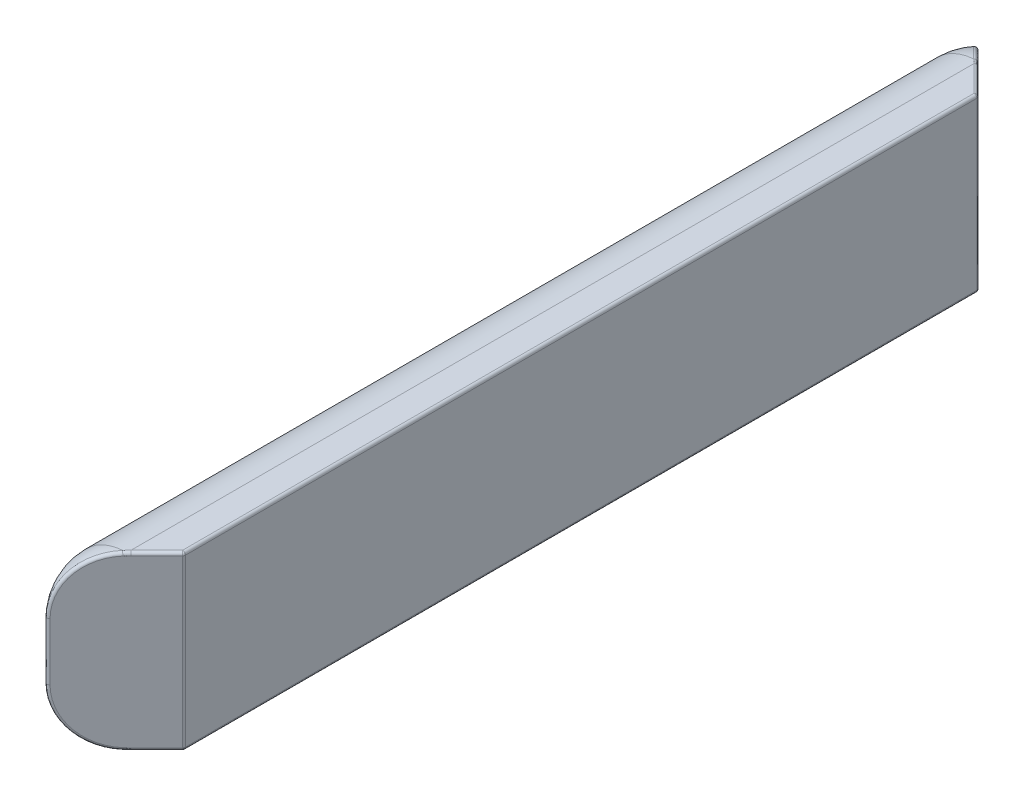
SolidWorks part; units mm, degrees
ref_plane "Front Plane" through (0, 0, 0) normal (0, 0, 1) x (1, 0, 0)
ref_plane "Top Plane" through (0, 0, 0) normal (0, 1, 0) x (1, 0, 0)
ref_plane "Right Plane" through (0, 0, 0) normal (1, 0, 0) x (0, 0, -1)
sketch "Sketch1" plane through (0, 0, 0) normal (0, 1, 0) x (1, 0, 0)
  line L1 (-463.55, -427.99) -> (463.55, -427.99)
  line L2 (-463.55, -427.99) -> (-463.55, 427.99)
  line L3 (-463.55, 427.99) -> (463.55, 427.99)
  line L4 (463.55, -427.99) -> (463.55, 427.99)
  line L5 (-463.55, -427.99) -> (463.55, 427.99) construction
  line L6 (-463.55, 427.99) -> (463.55, -427.99) construction
  point P0 (0, 0)
  dimension "D1" = 855.98
  dimension "D2" = 927.1
extrude "Boss-Extrude1" add sketch "Sketch1" along normal blind 152.4
fillet "Fillet1" radius 50.8 12 edges at (0, 152.4, -427.99) (0, 0, -427.99) (-463.55, 76.2, -427.99) (-463.55, 152.4, 0) (-463.55, 0, 0) (463.55, 152.4, 0) (463.55, 76.2, -427.99) (463.55, 0, 0) (-463.55, 76.2, 427.99) (0, 152.4, 427.99) (463.55, 76.2, 427.99) (0, 0, 427.99)
sketch "Sketch3" plane through (0, 152.4, 0) normal (0, 1, 0) x (1, 0, 0)
  line L0 (-412.75, 427.99) -> (412.75, 427.99) construction
  line L1 (-387.35, -351.79) -> (387.35, -351.79)
  line L2 (-387.35, -351.79) -> (-387.35, 351.79)
  line L3 (-387.35, 351.79) -> (387.35, 351.79)
  line L4 (387.35, -351.79) -> (387.35, 351.79)
  line L5 (-387.35, -351.79) -> (387.35, 351.79) construction
  line L6 (-387.35, 351.79) -> (387.35, -351.79) construction
  line L7 (-463.55, -377.19) -> (-463.55, 377.19) construction
  point P0 (0, 0)
  dimension "D1" = 76.2
  dimension "D2" = 76.2
extrude "Cut-Extrude1" cut sketch "Sketch3" against normal blind 152.4
sketch "Sketch4" plane through (0, 152.4, 0) normal (0, 1, 0) x (1, 0, 0)
  line L0 (-387.35, 351.79) -> (-463.55, 427.99)
  line L1 (-463.55, 427.99) -> (463.55, 427.99)
  line L2 (463.55, 427.99) -> (463.55, -427.99)
  line L3 (463.55, -427.99) -> (-463.55, -427.99)
  line L4 (-463.55, -427.99) -> (-387.35, -351.79)
  line L5 (-387.35, -351.79) -> (-387.35, 351.79)
  line L7 (-387.35, -351.79) -> (387.35, -351.79) construction
  line L8 (387.35, -351.79) -> (387.35, 351.79) construction
  line L9 (387.35, 351.79) -> (-387.35, 351.79) construction
  dimension "D1" = 45
  dimension "D2" = 45
  dimension "D3" = 76.2
  dimension "D4" = 76.2
  dimension "D5" = 76.2
extrude "Cut-Extrude2" cut sketch "Sketch4" against normal through all
fillet "Fillet2" radius 2.54 14 edges at (-400.05, 152.4, 364.49) (-438.15, 137.521, 402.59) (-448.671, 76.2, 413.111) (-438.15, 14.879, 402.59) (-400.05, 0, -364.49) (-400.05, 152.4, -364.49) (-438.15, 137.521, -402.59) (-448.671, 76.2, -413.111) (-438.15, 14.879, -402.59) (-387.35, 76.2, -351.79) (-387.35, 0, 0) (-387.35, 76.2, 351.79) (-387.35, 152.4, 0) (-400.05, 0, 364.49)
